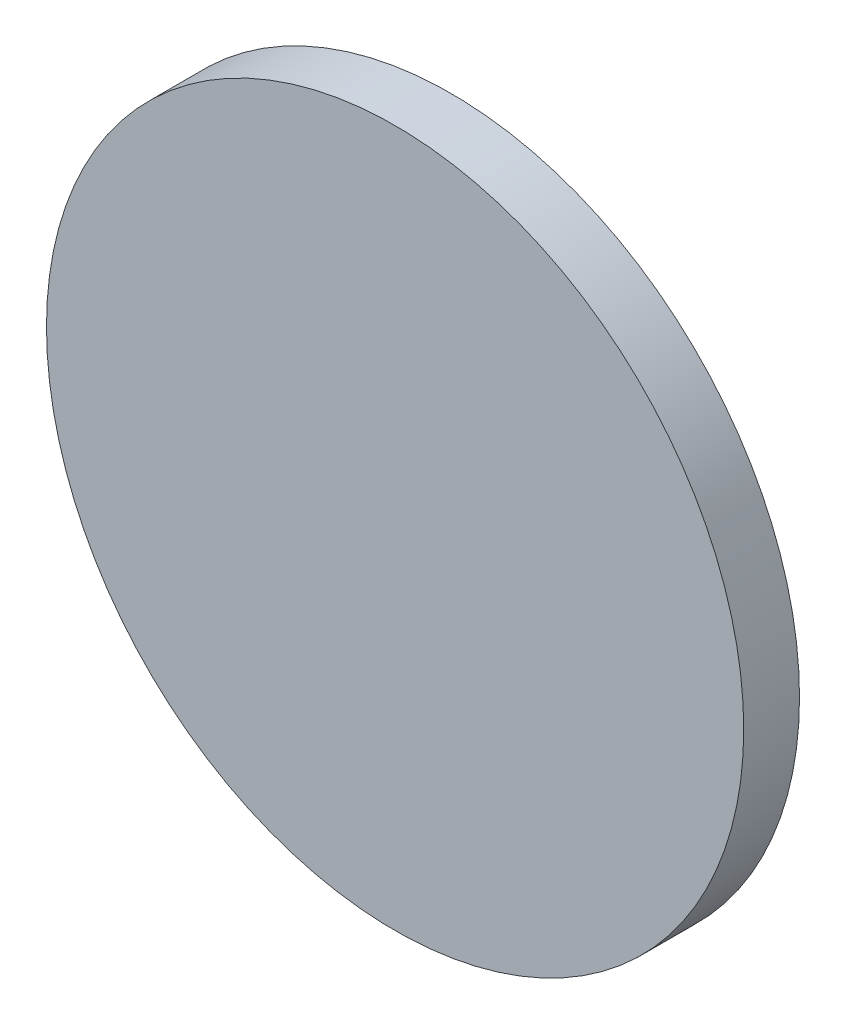
SolidWorks part; units mm, degrees
ref_plane "前视基准面" through (0, 0, 0) normal (0, 0, 1) x (1, 0, 0)
ref_plane "上视基准面" through (0, 0, 0) normal (0, 1, 0) x (1, 0, 0)
ref_plane "右视基准面" through (0, 0, 0) normal (1, 0, 0) x (0, 0, -1)
sketch "草图1" plane through (0, 0, 0) normal (0, 0, 1) x (1, 0, 0)
  circle A0 centre (0, 0) radius 12.5
  dimension "D1" = 25
extrude "凸台-拉伸1" add sketch "草图1" along normal blind 2 contours A0
